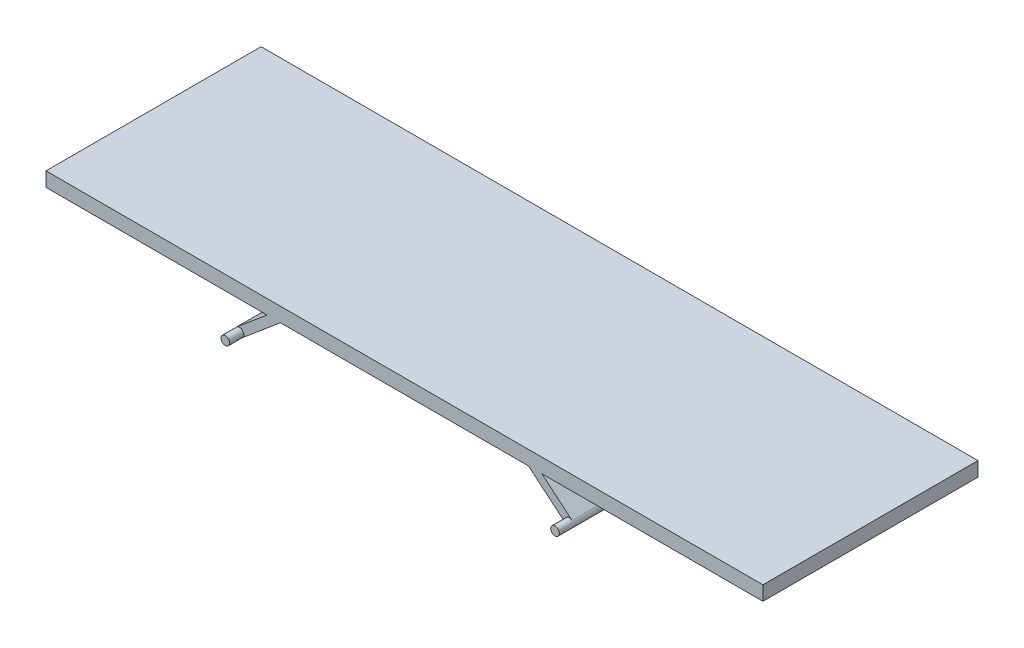
SolidWorks part; units mm, degrees
ref_plane "Front Plane" through (0, 0, 0) normal (0, 0, 1) x (1, 0, 0)
ref_plane "Top Plane" through (0, 0, 0) normal (0, 1, 0) x (1, 0, 0)
ref_plane "Right Plane" through (0, 0, 0) normal (1, 0, 0) x (0, 0, -1)
sketch "Sketch1" plane through (0, 0, 0) normal (0, 0, 1) x (1, 0, 0)
  line L0 (-233.8567, -45.4037) -> (-191.6642, -10)
  line L1 (500, -10) -> (191.6642, -10)
  line L2 (500, -10) -> (500, 10)
  line L3 (500, 10) -> (-500, 10)
  line L4 (-500, -10) -> (-500, 10)
  line L5 (500, -10) -> (-500, 10) construction
  line L6 (500, 10) -> (-500, -10) construction
  line L7 (-226.1433, -54.5963) -> (-172.9955, -10)
  line L8 (226.1433, -54.5963) -> (172.9955, -10)
  line L9 (233.8567, -45.4037) -> (191.6642, -10)
  line L10 (-191.6642, -10) -> (-500, -10)
  line L11 (172.9955, -10) -> (-172.9955, -10)
  arc A0 (-233.8567, -45.4037) -> (-226.1433, -54.5963) centre (-230, -50) ccw
  arc A1 (226.1433, -54.5963) -> (233.8567, -45.4037) centre (230, -50) ccw
  point P0 (0, 0)
  dimension "D3" = 230
  dimension "D5" = 12
  dimension "D6" = 12
  dimension "D8" = 50
  dimension "D1" = 1000
  dimension "D2" = 20
  dimension "D4" = 230
  dimension "D7" = 50
  dimension "D9" = 40
  dimension "D10" = 40
  dimension "D11" = 40
  dimension "D12" = 40
extrude "Boss-Extrude1" add sketch "Sketch1" along normal blind 300
sketch "Sketch2" plane through (0, 0, 300) normal (0, 0, 1) x (1, 0, 0)
  circle A0 centre (-230, -50) radius 6
  circle A1 centre (230, -50) radius 6
extrude "Boss-Extrude2" add sketch "Sketch2" along normal blind 20
